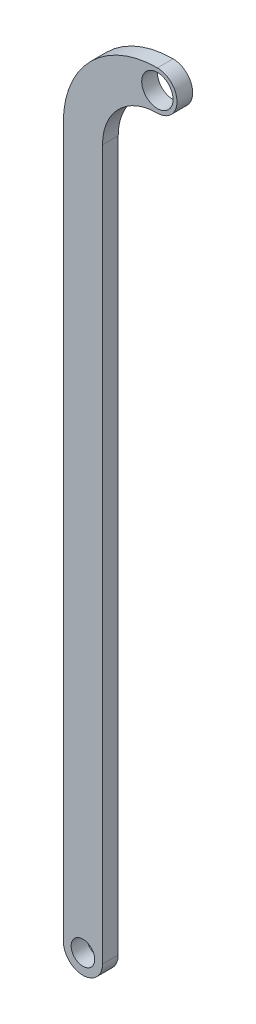
SolidWorks part; units mm, degrees
ref_plane "Front Plane" through (0, 0, 0) normal (0, 0, 1) x (1, 0, 0)
ref_plane "Top Plane" through (0, 0, 0) normal (0, 1, 0) x (1, 0, 0)
ref_plane "Right Plane" through (0, 0, 0) normal (1, 0, 0) x (0, 0, -1)
sketch "Sketch2" plane through (0, 0, 0) normal (0, 0, 1) x (1, 0, 0)
  line L0 (-6, -4.75) -> (-6, -50)
  line L2 (-3.5, -50) -> (-3.5, -4.75)
  circle A0 centre (0, 0) radius 1
  arc A1 (0, -1.25) -> (0, 1.25) centre (0, 0) ccw
  arc A2 (0, 1.25) -> (-6, -4.75) centre (0, -4.75) ccw
  arc A3 (0, -1.25) -> (-3.5, -4.75) centre (0, -4.75) ccw
  circle A4 centre (-4.75, -50) radius 0.75
  arc A5 (-6, -50) -> (-3.5, -50) centre (-4.75, -50) ccw
  circle A6 centre (-4.75, -50) radius 1.25 construction
  dimension "D1" = 2
  dimension "D2" = 2.5
  dimension "D4" = 1.5
  dimension "D3" = 2.5
  dimension "D5" = 50
  dimension "D6" = 3.5
extrude "Boss-Extrude1" add sketch "Sketch2" along normal blind 1
